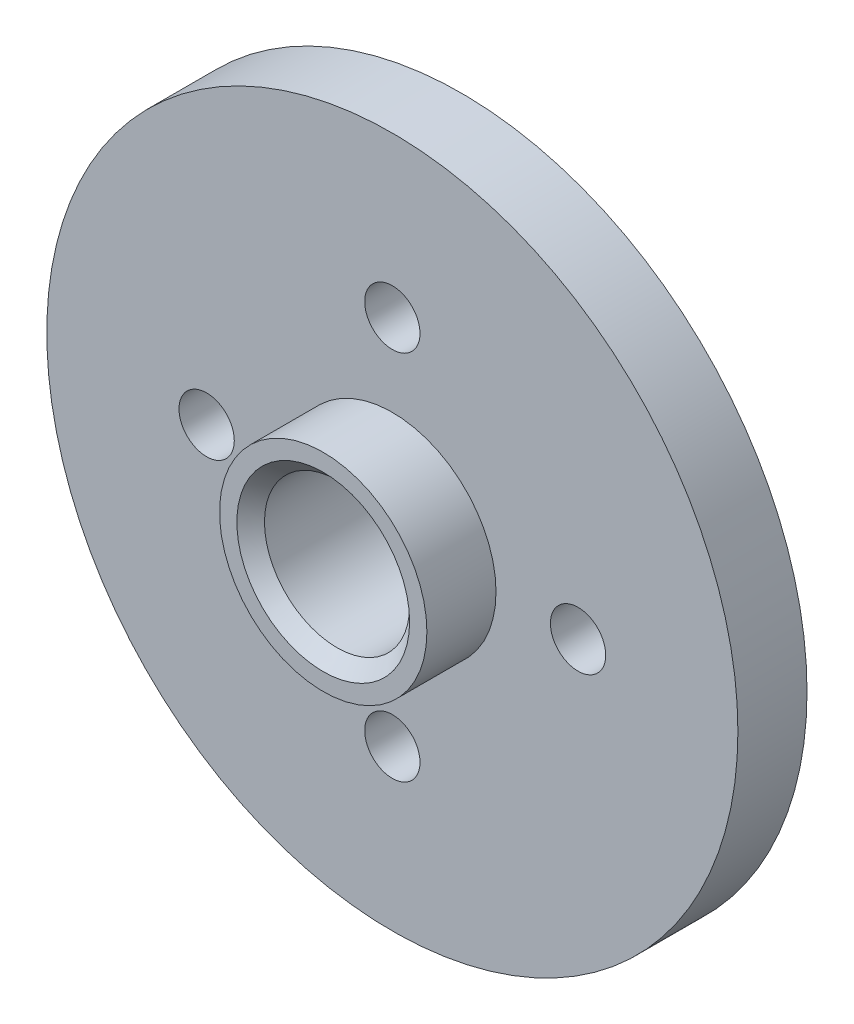
SolidWorks part; units mm, degrees
material "Lega 1060"
ref_plane "Piano frontale" through (0, 0, 0) normal (0, 0, 1) x (1, 0, 0)
ref_plane "Piano superiore" through (0, 0, 0) normal (0, 1, 0) x (1, 0, 0)
ref_plane "Piano destro" through (0, 0, 0) normal (1, 0, 0) x (0, 0, -1)
sketch "Schizzo1" plane through (0, 0, 0) normal (0, 0, 1) x (1, 0, 0)
  circle A0 centre (0, 0) radius 50
  circle A1 centre (0, 26.8701) radius 4
  circle A3 centre (26.8701, 0) radius 4
  circle A4 centre (0, -26.8701) radius 4
  circle A5 centre (-26.8701, 0) radius 4
  dimension "D1" = 100
  dimension "D3" = 8
  dimension "D5" = 38
  dimension "D4" = 4
extrude "Estrusione-Estrusione1" add sketch "Schizzo1" along normal blind 10
sketch "Schizzo2" plane through (0, 0, 10) normal (0, 0, 1) x (1, 0, 0)
  circle A0 centre (0, 0) radius 15
  dimension "D1" = 30
extrude "Estrusione-Estrusione2" add sketch "Schizzo2" along normal blind 10
hole_wizard "Foro filettato M24-1" positions "Schizzo7" profile "Schizzo6" tap size "M24" standard "ISO" end condition through all
sketch "Schizzo7" plane through (0, 0, 0) normal (0, 0, -1) x (-1, 0, 0)
  point P0 (0, 0)
sketch "Schizzo6" plane through (0, 0, 0) normal (1, 0, 0) x (0, 1, 0)
  line L0 (0, 0) -> (0, 20)
  line L1 (0, 20) -> (10.5, 20)
  line L2 (10.5, 20) -> (10.5, 0.8805)
  line L3 (10.5, 0.8805) -> (12.025, 0)
  line L5 (12.025, 0) -> (0, 0)
  line L6 (-10.5, 0.8805) -> (-12.025, 0) construction
  line L11 (0, -6.35) -> (0, 107.95) construction
  dimension "Thru Tap Drill Dia." = 21
  dimension "Thru Tap Drill Depth" = 20
  dimension "Near C'Sink Dia." = 24.05
  dimension "Near C'Sink Angle" = 120
cosmetic thread "Filettatura del foro2" parameters "D2"=24
chamfer "Smusso1" distance 2 angle 45 1 edges at (-10.5, 0, 20)
